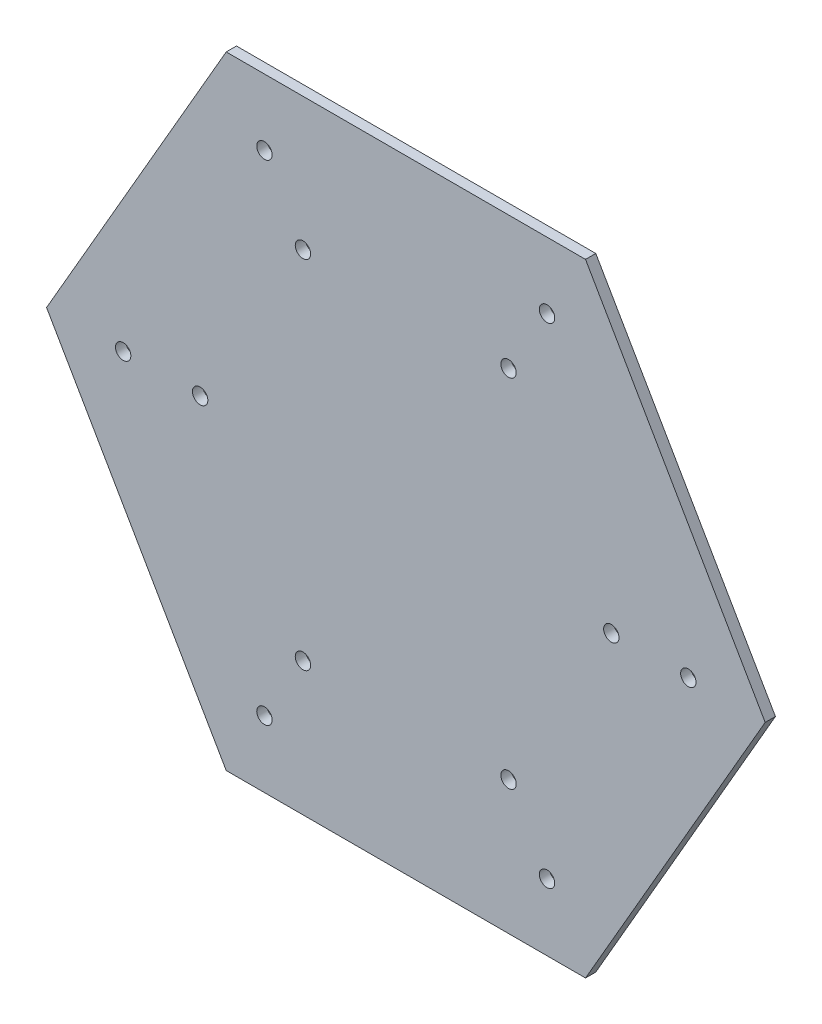
SolidWorks part; units mm, degrees
ref_plane "Front Plane" through (0, 0, 0) normal (0, 0, 1) x (1, 0, 0)
ref_plane "Top Plane" through (0, 0, 0) normal (0, 1, 0) x (1, 0, 0)
ref_plane "Right Plane" through (0, 0, 0) normal (1, 0, 0) x (0, 0, -1)
sketch "Sketch2" plane through (0, 0, 0) normal (0, 0, 1) x (1, 0, 0)
  line L1 (35, -60.6218) -> (70, 0)
  line L2 (70, 0) -> (35, 60.6218)
  line L3 (35, 60.6218) -> (-35, 60.6218)
  line L4 (-35, 60.6218) -> (-70, 0)
  line L5 (-70, 0) -> (-35, -60.6218)
  line L6 (-35, -60.6218) -> (35, -60.6218)
  circle A0 centre (0, 0) radius 60.6218 construction
  dimension "D1" = 70
  dimension "D2" = 70
extrude "Boss-Extrude1" add sketch "Sketch2" along normal blind 2
sketch "Sketch3" plane through (0, 0, 0) normal (0, 0, 1) x (1, 0, 0)
  circle A0 centre (27.5, -47.6314) radius 1.5
  circle A1 centre (20, -34.641) radius 1.5
  dimension "D2" = 15
extrude "Cut-Extrude1" cut sketch "Sketch3" along normal blind 2
sketch "Sketch4" plane through (0, 0, 0) normal (0, 0, 1) x (1, 0, 0)
  circle A0 centre (0, 0) radius 1.9736
pattern_circular "CirPattern1" count 6 every 60 about axis through (-0.0264, 0.0457, 0) along (0, 0, 1) of "Cut-Extrude1"
